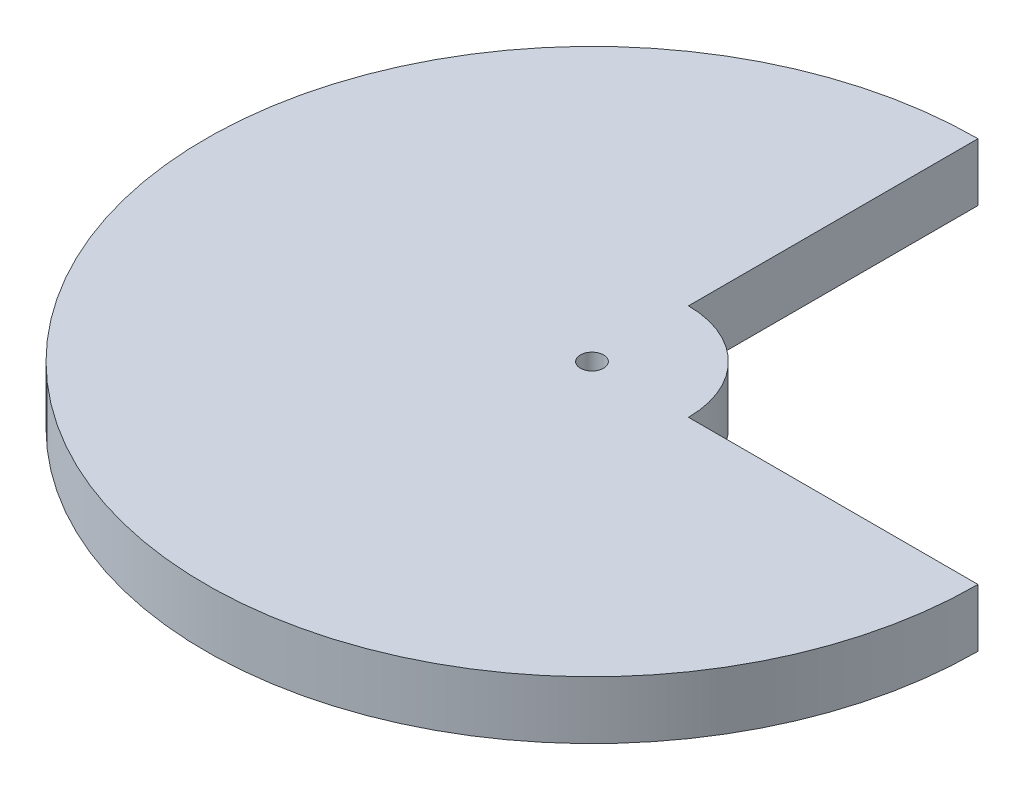
SolidWorks part; units mm, degrees
ref_plane "前视基准面" through (0, 0, 0) normal (0, 0, 1) x (1, 0, 0)
ref_plane "上视基准面" through (0, 0, 0) normal (0, 1, 0) x (1, 0, 0)
ref_plane "右视基准面" through (0, 0, 0) normal (1, 0, 0) x (0, 0, -1)
sketch "草图1" plane through (0, 0, 0) normal (0, 1, 0) x (1, 0, 0)
  line L1 (0, 5) -> (0, 20)
  line L2 (20, 0) -> (5, 0)
  arc A0 (0, 20) -> (20, 0) centre (0, 0) ccw
  arc A1 (5, 0) -> (0, 5) centre (0, 0) ccw
  circle A2 centre (0, 0) radius 0.6
  dimension "D1" = 20
  dimension "D2" = 1.2
  dimension "D3" = 5
extrude "凸台-拉伸1" add sketch "草图1" along normal blind 3
